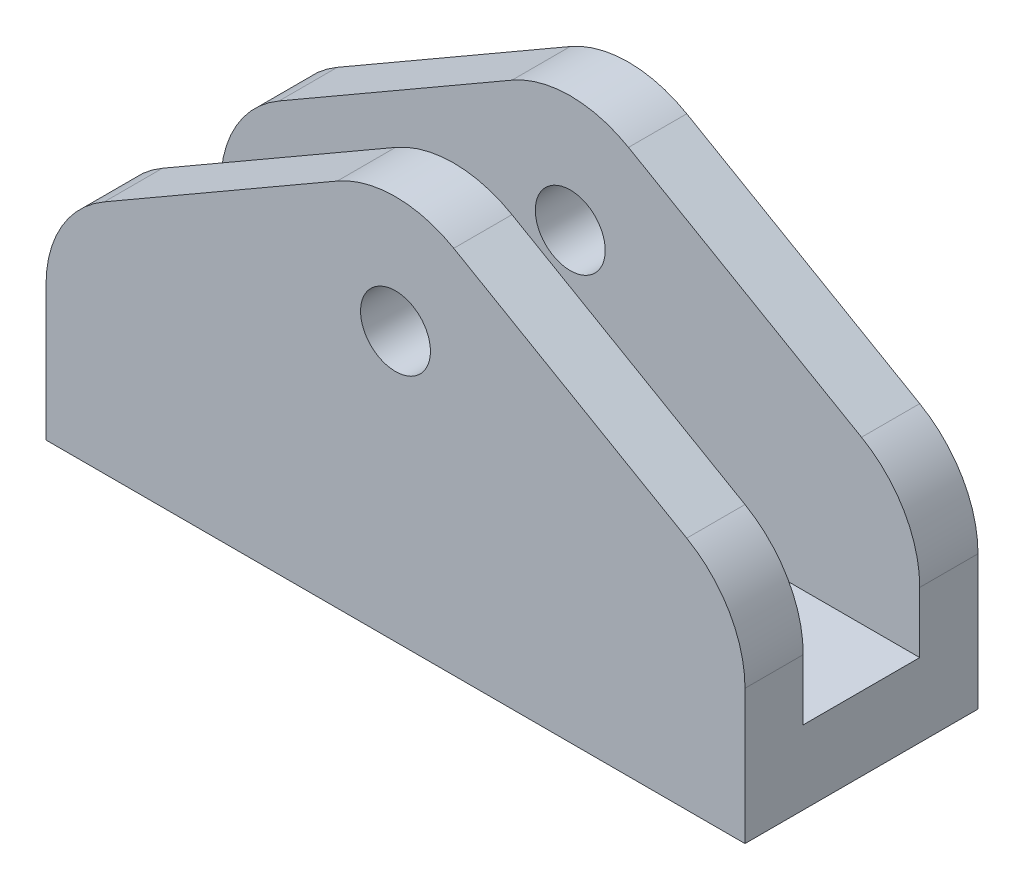
SolidWorks part; units mm, degrees
ref_plane "Front Plane" through (0, 0, 0) normal (0, 0, 1) x (1, 0, 0)
ref_plane "Top Plane" through (0, 0, 0) normal (0, 1, 0) x (1, 0, 0)
ref_plane "Right Plane" through (0, 0, 0) normal (1, 0, 0) x (0, 0, -1)
sketch "Sketch1" plane through (0, 0, 0) normal (0, 0, 1) x (1, 0, 0)
  line L1 (0, -17.3205) -> (15, -8.6603)
  line L2 (15, -8.6603) -> (15, 8.6603)
  line L3 (15, 8.6603) -> (0, 17.3205)
  line L4 (0, 17.3205) -> (-15, 8.6603)
  line L5 (-15, 8.6603) -> (-15, -8.6603)
  line L6 (-15, -8.6603) -> (0, -17.3205)
  circle A0 centre (0, 0) radius 15 construction
  dimension "D1" = 30
extrude "Boss-Extrude1" add sketch "Sketch1" along normal mid plane 10
sketch "Sketch2" plane through (0, 0, 5) normal (0, 0, 1) x (1, 0, 0)
  line L0 (-15, 0) -> (15, 0)
  line L1 (-15, 8.6603) -> (-15, -8.6603) construction
  line L2 (15, -8.6603) -> (15, 8.6603) construction
  line L3 (15, 0) -> (15, -19.4603)
  line L4 (15, -19.4603) -> (-15, -19.4603)
  line L5 (-15, -19.4603) -> (-15, 0)
extrude "Cut-Extrude1" cut sketch "Sketch2" against normal through all
fillet "Fillet1" radius 5 3 edges at (15, 8.6603, 0) (0, 17.3205, 0) (-15, 8.6603, 0)
sketch "Sketch3" plane through (0, 0, 5) normal (0, 0, 1) x (1, 0, 0)
  circle A0 centre (0, 11.547) radius 1.5
  dimension "D1" = 3
extrude "Cut-Extrude2" cut sketch "Sketch3" against normal through all
sketch "Sketch4" plane through (0, 0, 0) normal (1, 0, 0) x (0, 0, -1)
  line L0 (0, 0) -> (0, 16.547) construction
  line L1 (5, 16.547) -> (-5, 16.547) construction
  line L3 (-2.5, 29.9291) -> (2.5, 29.9291)
  line L4 (-2.5, 29.9291) -> (-2.5, 3.165)
  line L5 (-2.5, 3.165) -> (2.5, 3.165)
  line L6 (2.5, 29.9291) -> (2.5, 3.165)
  line L7 (-2.5, 29.9291) -> (2.5, 3.165) construction
  line L8 (-2.5, 3.165) -> (2.5, 29.9291) construction
  dimension "D1" = 5
extrude "Cut-Extrude3" cut sketch "Sketch4" against normal through all both and the other way through all
